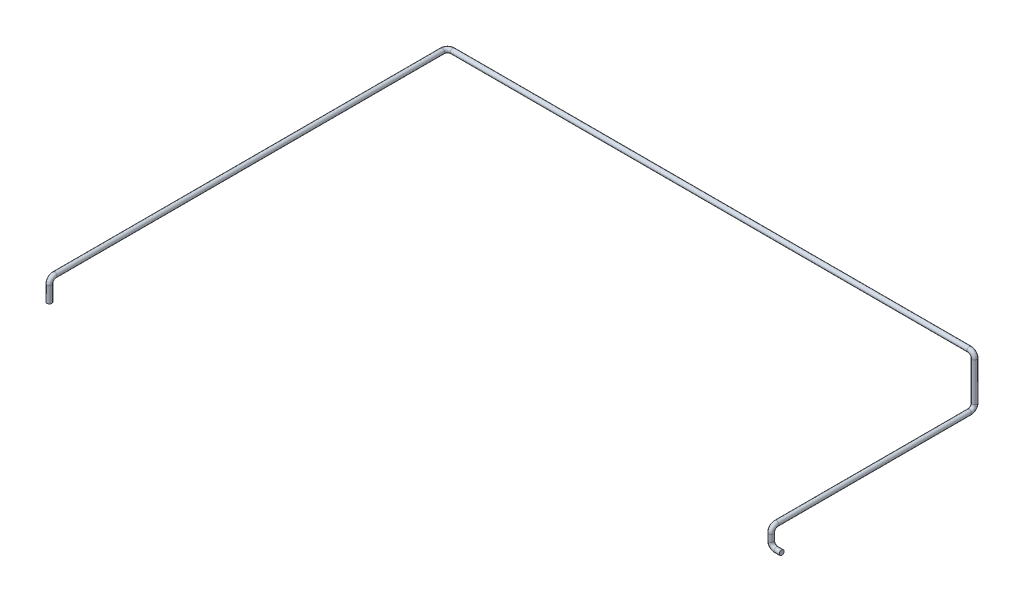
SolidWorks part; units mm, degrees
ref_plane "Alzado" through (0, 0, 0) normal (0, 0, 1) x (1, 0, 0)
ref_plane "Planta" through (0, 0, 0) normal (0, 1, 0) x (1, 0, 0)
ref_plane "Vista lateral" through (0, 0, 0) normal (1, 0, 0) x (0, 0, -1)
sketch3d "Croquis3D1"
  line L0 (0, 0, 0) -> (-30, 0, 0)
  line L1 (-60, 30, 0) -> (-60, 70, 0)
  line L2 (-60, 100, -30) -> (-60, 100, -1130)
  line L6 (-60, 130, -1160) -> (-60, 350, -1160)
  line L7 (-90, 380, -1160) -> (-3035, 380, -1160)
  line L8 (-3065, 380, -1130) -> (-3065, 380, 1080)
  line L9 (-3065, 350, 1110) -> (-3065, 260, 1110)
  arc A0 (-3065, 380, 1080) -> (-3065, 350, 1110) centre (-3065, 350, 1080) ccw
  arc A1 (-3035, 380, -1160) -> (-3065, 380, -1130) centre (-3035, 380, -1130) ccw
  arc A2 (-60, 350, -1160) -> (-90, 380, -1160) centre (-90, 350, -1160) ccw
  arc A3 (-60, 130, -1160) -> (-60, 100, -1130) centre (-60, 130, -1130) ccw
  arc A4 (-60, 70, 0) -> (-60, 100, -30) centre (-60, 70, -30) ccw
  arc A5 (-30, 0, 0) -> (-60, 30, 0) centre (-30, 30, 0) ccw
  point P6 (-3065, 380, 1110)
  point P11 (-3035, 350, 1080)
  point P15 (-3065, 380, -1160)
  point P16 (-3035, 410, -1130)
  point P19 (-60, 380, -1160)
  point P20 (-90, 350, -1130)
  point P23 (-60, 100, -1160)
  point P24 (-90, 130, -1130)
  point P27 (-60, 100, 0)
  point P28 (-90, 70, -30)
  point P31 (-60, 0, 0)
  point P32 (-30, 30, -30)
  dimension "D8" = 30
  dimension "D1" = 60
  dimension "D2" = 100
  dimension "D3" = 1160
  dimension "D4" = 280
  dimension "D5" = 3005
  dimension "D6" = 2270
  dimension "D7" = 120
sketch "Croquis1" plane through (0, 0, 0) normal (1, 0, 0) x (0, 0, -1)
  circle A0 centre (0, 0) radius 13.7
  dimension "D1" = 27.4
sweep "Barrer1" add profiles "Croquis1" path "Croquis3D1"
